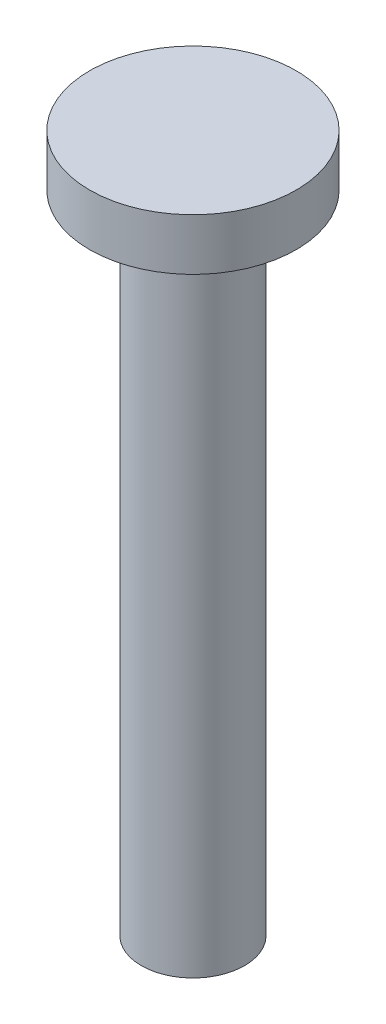
SolidWorks part; units mm, degrees
ref_plane "Front Plane" through (0, 0, 0) normal (0, 0, 1) x (1, 0, 0)
ref_plane "Top Plane" through (0, 0, 0) normal (0, 1, 0) x (1, 0, 0)
ref_plane "Right Plane" through (0, 0, 0) normal (1, 0, 0) x (0, 0, -1)
sketch "Sketch1" plane through (0, 0, 0) normal (0, 1, 0) x (1, 0, 0)
  circle A0 centre (0, 0) radius 1
  dimension "D1" = 2
extrude "Boss-Extrude1" add sketch "Sketch1" along normal blind 12.5
sketch "Sketch2" plane through (0, 12.5, 0) normal (0, 1, 0) x (1, 0, 0)
  circle A0 centre (0, 0) radius 2
  dimension "D1" = 4
extrude "Boss-Extrude2" add sketch "Sketch2" along normal blind 1
